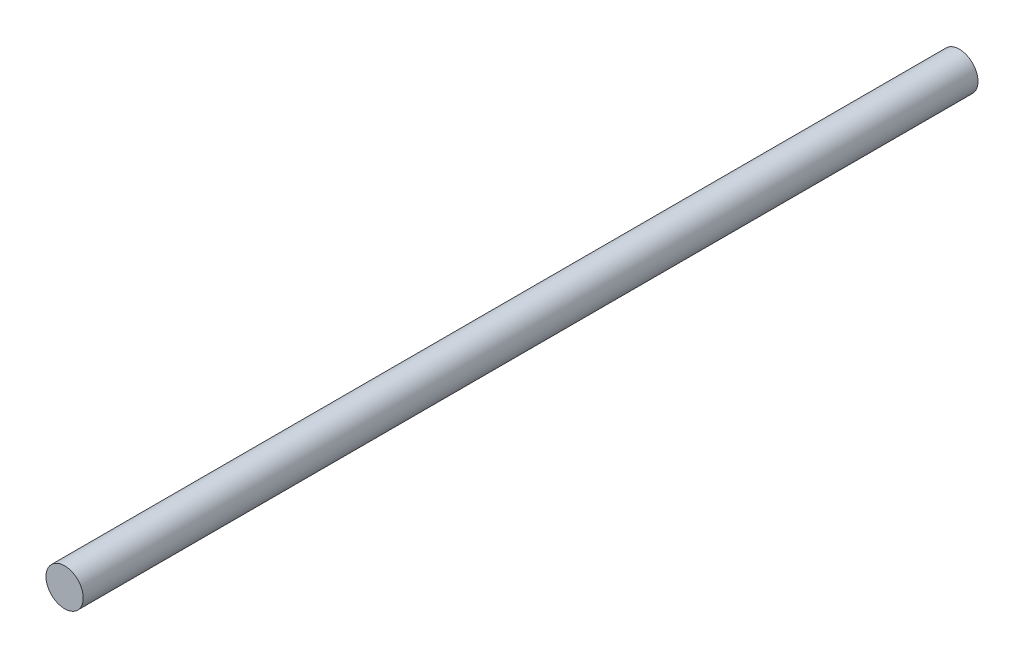
SolidWorks part; units mm, degrees
ref_plane "Front Plane" through (0, 0, 0) normal (0, 0, 1) x (1, 0, 0)
ref_plane "Top Plane" through (0, 0, 0) normal (0, 1, 0) x (1, 0, 0)
ref_plane "Right Plane" through (0, 0, 0) normal (1, 0, 0) x (0, 0, -1)
sketch "Sketch1" plane through (0, 0, 0) normal (0, 0, 1) x (1, 0, 0)
  circle A0 centre (0, 0) radius 2.5
  dimension "D1" = 5
extrude "Boss-Extrude1" add sketch "Sketch1" along normal blind 120
